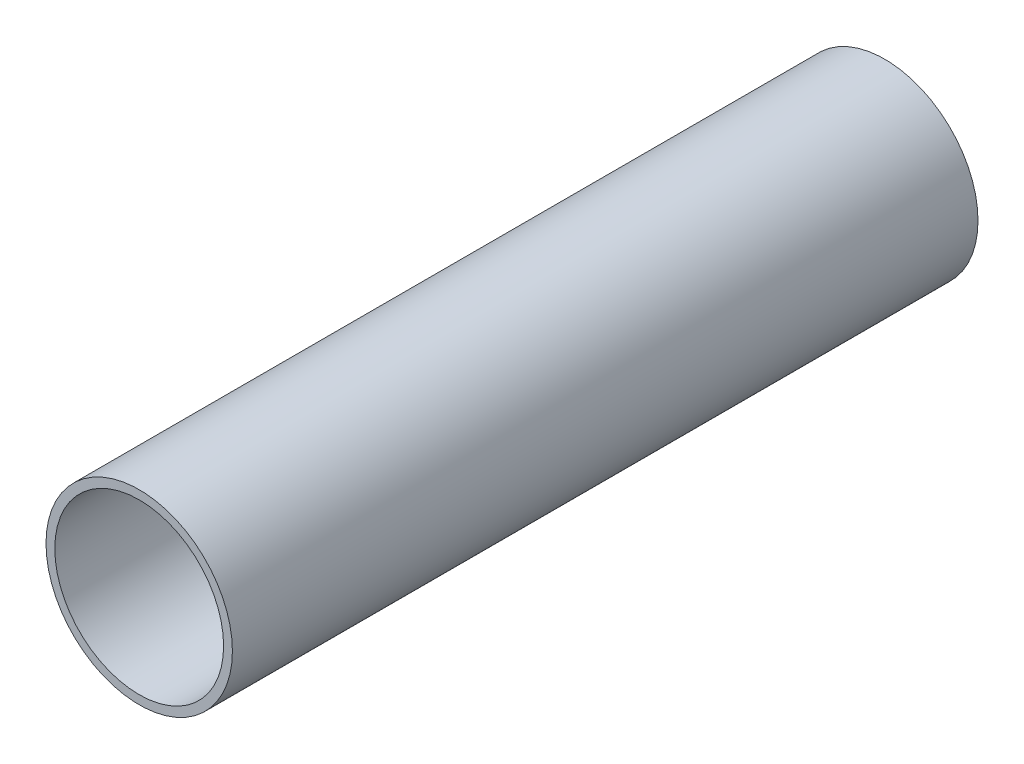
SolidWorks part; units mm, degrees
material "PVC Rigid"
ref_plane "Front Plane" through (0, 0, 0) normal (0, 0, 1) x (1, 0, 0)
ref_plane "Top Plane" through (0, 0, 0) normal (0, 1, 0) x (1, 0, 0)
ref_plane "Right Plane" through (0, 0, 0) normal (1, 0, 0) x (0, 0, -1)
sketch "Sketch1" plane through (0, 0, 0) normal (0, 0, 1) x (1, 0, 0)
  circle A0 centre (0, 0) radius 76.2
  circle A1 centre (0, 0) radius 84.1375
  dimension "D1" = 152.4
  dimension "D2" = 168.275
extrude "Boss-Extrude1" add sketch "Sketch1" along normal blind 673.1
